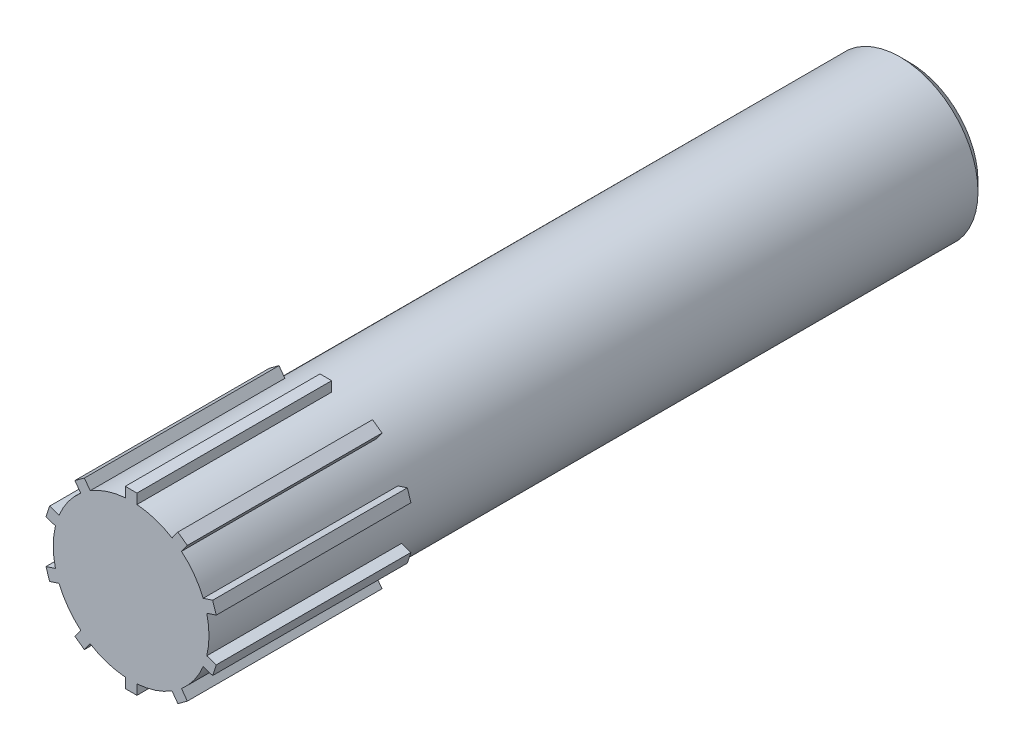
SolidWorks part; units mm, degrees
ref_plane "Front Plane" through (0, 0, 0) normal (0, 0, 1) x (1, 0, 0)
ref_plane "Top Plane" through (0, 0, 0) normal (0, 1, 0) x (1, 0, 0)
ref_plane "Right Plane" through (0, 0, 0) normal (1, 0, 0) x (0, 0, -1)
sketch "Sketch1" plane through (0, 0, 0) normal (0, 0, 1) x (1, 0, 0)
  circle A0 centre (0, 0) radius 4
  dimension "D1" = 8
extrude "Boss-Extrude1" add sketch "Sketch1" along normal blind 40
sketch "Sketch2" plane through (0, 0, 0) normal (0, 1, 0) x (1, 0, 0)
  line L0 (0, 0) -> (0, -40) construction
  line L1 (-4, -40) -> (4, -40) construction
  line L2 (0, -5) -> (0, -9) construction
  line L3 (1.5, -5) -> (1.5, -9)
  line L4 (-1.5, -5) -> (-1.5, -9)
  arc A0 (1.5, -5) -> (-1.5, -5) centre (0, -5) ccw
  arc A1 (-1.5, -9) -> (1.5, -9) centre (0, -9) ccw
  point P7 (0, -7)
  dimension "D1" = 1.5
  dimension "D2" = 4
  dimension "D3" = 5
extrude "Cut-Extrude1" cut sketch "Sketch2" against normal through all from offset 2.5 offset against normal yes
sketch "Sketch3" plane through (0, 0, 40) normal (0, 0, 1) x (1, 0, 0)
  line L0 (0, 0) -> (0, 5.3811) construction
  line L2 (-0.3, 4.5) -> (0.3, 4.5)
  line L3 (-0.3, 4.5) -> (-0.3, 1.9417)
  line L4 (-0.3, 1.9417) -> (0.3, 1.9417)
  line L5 (0.3, 4.5) -> (0.3, 1.9417)
  line L6 (-0.3, 4.5) -> (0.3, 1.9417) construction
  line L7 (-0.3, 1.9417) -> (0.3, 4.5) construction
  point P3 (0, 3.2208)
  point P8 (0, 4.5)
  dimension "D1" = 0.6
  dimension "D2" = 4.5
extrude "Boss-Extrude2" add sketch "Sketch3" against normal blind 10
pattern_circular "CirPattern1" count 10 over 360 about axis through (0, 0, 0) along (0, 0, 1) of "Boss-Extrude2"
chamfer "Chamfer1" distance 0.5 angle 45 1 edges at (4, 0, 0)
